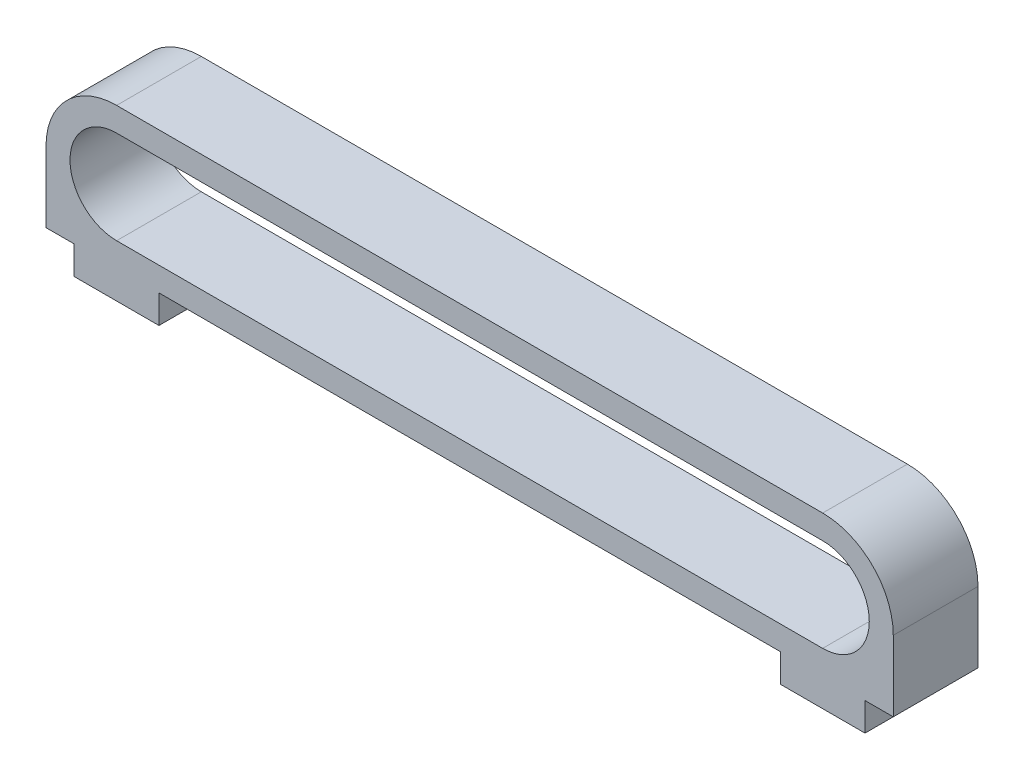
SolidWorks part; units mm, degrees
ref_plane "Front Plane" through (0, 0, 0) normal (0, 0, 1) x (1, 0, 0)
ref_plane "Top Plane" through (0, 0, 0) normal (0, 1, 0) x (1, 0, 0)
ref_plane "Right Plane" through (0, 0, 0) normal (1, 0, 0) x (0, 0, -1)
sketch "Sketch1" plane through (0, 0, 0) normal (0, 0, 1) x (1, 0, 0)
  line L0 (-12.5, 0) -> (12.5, 0) construction
  line L1 (-12.5, 1.65) -> (12.5, 1.65)
  line L2 (-12.5, -1.65) -> (12.5, -1.65)
  line L3 (-12.5, 0) -> (12.5, 0) construction
  line L4 (-12.5, 2.5) -> (12.5, 2.5)
  line L5 (-12.5, -2.5) -> (12.5, -2.5)
  arc A0 (-12.5, 1.65) -> (-12.5, -1.65) centre (-12.5, 0) ccw
  arc A1 (12.5, -1.65) -> (12.5, 1.65) centre (12.5, 0) ccw
  arc A2 (-12.5, 2.5) -> (-12.5, -2.5) centre (-12.5, 0) ccw
  arc A3 (12.5, -2.5) -> (12.5, 2.5) centre (12.5, 0) ccw
  point P2 (0, 0)
  point P10 (0, 0)
  point P15 (9.5556, 0)
  dimension "D1" = 1.65
  dimension "D2" = 2.5
  dimension "D3" = 25
extrude "Boss-Extrude1" add sketch "Sketch1" along normal mid plane 3
sketch "Sketch2" plane through (0, 0, 1.5) normal (0, 0, 1) x (1, 0, 0)
  line L0 (-15, 0) -> (-15, -2.5)
  line L1 (-15, -2.5) -> (-12.5, -2.5)
  line L2 (12.5, -2.5) -> (15, -2.5)
  line L3 (-12.5, -2.5) -> (12.5, -2.5) construction
  line L4 (15, -2.5) -> (15, 0)
  arc A0 (-12.5, 2.5) -> (-12.5, -2.5) centre (-12.5, 0) ccw construction
  arc A1 (12.5, -2.5) -> (12.5, 2.5) centre (12.5, 0) ccw construction
  arc A2 (-15, 0) -> (-12.5, -2.5) centre (-12.5, 0) ccw
  arc A3 (12.5, -2.5) -> (15, 0) centre (12.5, 0) ccw
  point P4 (10.85, -2.5)
  point P5 (0, 0)
  point P12 (13.35, -2.5)
  point P13 (8.3619, 0.2434)
  point P17 (0, 0)
  point P18 (0, 0)
  point P19 (13.35, -2.5)
  point P20 (-12.2815, -2.0496)
  point P23 (-13.35, 0)
  point P24 (-13.35, -2.5)
extrude "Boss-Extrude2" add sketch "Sketch2" against normal blind 3
sketch "Sketch3" plane through (0, -2.5, 0) normal (0, -1, 0) x (1, 0, 0)
  line L0 (-15, 1.5) -> (15, 1.5) construction
  line L1 (-14, 1.5) -> (-11, 1.5)
  line L2 (-14, 1.5) -> (-14, -1.5)
  line L3 (-14, -1.5) -> (-11, -1.5)
  line L4 (-11, 1.5) -> (-11, -1.5)
  line L5 (-15, -1.5) -> (15, -1.5) construction
  line L6 (-14, 0) -> (14, 0) construction
  line L7 (14, 1.5) -> (11, 1.5)
  line L8 (14, 1.5) -> (14, -1.5)
  line L9 (14, -1.5) -> (11, -1.5)
  line L10 (11, 1.5) -> (11, -1.5)
  point P14 (0, 0)
  dimension "D1" = 25
extrude "Boss-Extrude3" add sketch "Sketch3" along normal blind 1
